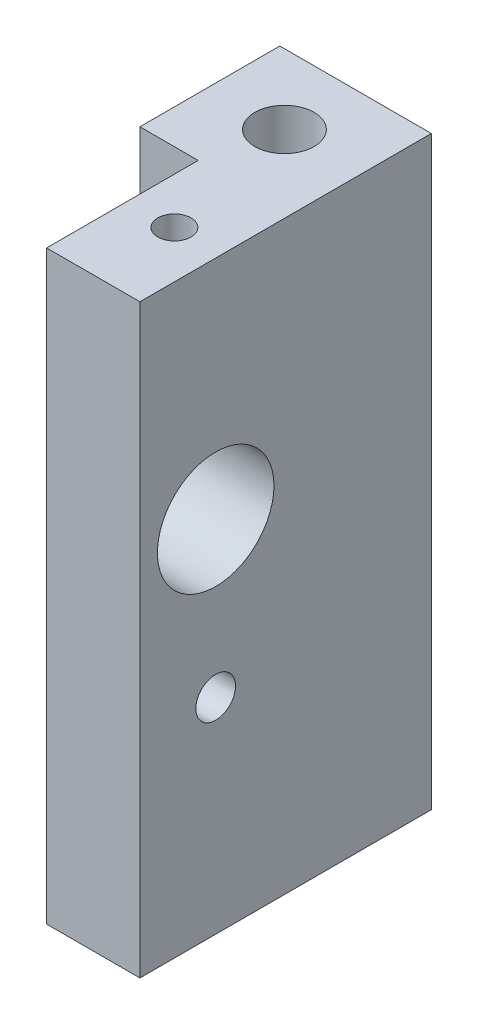
SolidWorks part; units mm, degrees
material "PET"
ref_plane "Front" through (0, 0, 0) normal (0, 0, 1) x (1, 0, 0)
ref_plane "Top" through (0, 0, 0) normal (0, 1, 0) x (1, 0, 0)
ref_plane "Right" through (0, 0, 0) normal (1, 0, 0) x (0, 0, -1)
sketch "Sketch1" plane through (0, 0, 0) normal (0, 1, 0) x (1, 0, 0)
  line L0 (0, 0) -> (-3.9688, 0)
  line L1 (-3.9688, 0) -> (-3.9688, 9.525)
  line L2 (-3.9688, 9.525) -> (6.35, 9.525)
  line L3 (6.35, 9.525) -> (6.35, -10.3187)
  line L4 (6.35, -10.3187) -> (0, -10.3187)
  line L5 (0, -10.3187) -> (0, 0)
  dimension "D2" = 9.525
  dimension "D3" = 19.8438
  dimension "D4" = 6.35
  dimension "D6" = 10.3187
extrude "Boss-Extrude1" add sketch "Sketch1" along normal blind 39.878
sketch "Sketch6" plane through (0, 39.878, 0) normal (0, 1, 0) x (1, 0, 0)
  line L16 (6.35, 9.525) -> (-3.9688, 9.525) construction
  line L17 (-3.9688, 9.525) -> (-3.9688, 0) construction
  point P0 (1.1112, 4.7625)
  dimension "D1" = 4.7625
  dimension "D2" = 5.08
hole_wizard "#10-32 Tapped Hole1" positions "Sketch6" profile "Sketch5" tap size "#10-32" standard "ANSI Inch" end condition up to next
sketch "Sketch5" plane through (1.1112, 39.878, -4.7625) normal (1, 0, 0) x (0, 0, 1)
  line L0 (0, 0) -> (0, 39.878)
  line L1 (0, 39.878) -> (2.0193, 39.878)
  line L2 (2.0193, 39.878) -> (2.0193, 0)
  line L5 (2.0193, 0) -> (0, 0)
  line L11 (0, -6.35) -> (0, 107.95) construction
  dimension "Thru Tap Drill Dia." = 4.0386
  dimension "Thru Tap Drill Depth" = 39.878
cosmetic thread "Hole Thread1" parameters "D2"=4.826
sketch "Sketch9" plane through (0, 0, 0) normal (-1, 0, 0) x (0, 0, 1)
  line L2 (0, 39.878) -> (0, 0) construction
  line L4 (10.3187, 39.878) -> (10.3187, 0) construction
  line L5 (0, 0) -> (10.3187, 0) construction
  line L6 (0, 13.9725) -> (5.1594, 13.9725) construction
  line L7 (5.1594, 13.9725) -> (10.3187, 13.9725) construction
  point P19 (5.1594, 13.9725)
  dimension "D2" = 13.9725
hole_wizard "#6-32 Tapped Hole1" positions "Sketch9" profile "Sketch8" tap size "#6-32" standard "ANSI Inch" end condition up to next
sketch "Sketch8" plane through (0, 13.9725, 5.1594) normal (0, 1, 0) x (0, 0, 1)
  line L0 (0, 0) -> (0, 6.35)
  line L1 (0, 6.35) -> (1.3525, 6.35)
  line L2 (1.3525, 6.35) -> (1.3525, 0)
  line L5 (1.3525, 0) -> (0, 0)
  line L11 (0, -6.35) -> (0, 107.95) construction
  dimension "Thru Tap Drill Dia." = 2.7051
  dimension "Thru Tap Drill Depth" = 6.35
cosmetic thread "Hole Thread3" parameters "D2"=3.5052
sketch "Sketch10" plane through (6.35, 0, 0) normal (1, 0, 0) x (0, 0, -1)
  circle A0 centre (-5.1594, 24.4725) radius 3.9688
  dimension "D1" = 7.9375
extrude "Cut-Extrude1" cut sketch "Sketch10" against normal up to next
sketch "Sketch14" plane through (0, 39.878, 0) normal (0, 1, 0) x (1, 0, 0)
  circle A2 centre (1.1112, 4.7625) radius 2.0193 construction
  point P0 (3.1432, -4.7625)
  dimension "D1" = 9.525
  dimension "D2" = 2.032
hole_wizard "#4-40 Tapped Hole1" positions "Sketch14" profile "Sketch12" tap size "#4-40" standard "ANSI Inch"
sketch "Sketch12" plane through (3.1432, 39.878, 4.7625) normal (1, 0, 0) x (0, 0, 1)
  line L0 (0, 0) -> (0, 7.0292)
  line L1 (0, 7.0292) -> (1.1303, 6.35)
  line L2 (1.1303, 6.35) -> (1.1303, 0)
  line L5 (1.1303, 0) -> (0, 0)
  line L10 (0, 7.0292) -> (-1.1303, 6.35) construction
  line L11 (0, -6.35) -> (0, 107.95) construction
  dimension "Tap Drill Dia." = 2.2606
  dimension "Tap Drill Depth" = 6.35
  dimension "Drill Angle" = 118
cosmetic thread "Hole Thread6" parameters "D1"=5.6896, "D2"=2.8448
mirror "Mirror1" [suppressed]
cosmetic thread "Hole Thread4" [suppressed] parameters "D2"=4.826
cosmetic thread "Hole Thread5" [suppressed] parameters "D2"=3.5052
cosmetic thread "Hole Thread7" [suppressed] parameters "D1"=5.6896, "D2"=2.8448
delete or keep bodies "Body-Delete/Keep 1" [suppressed] type delete bodies bodies 115
